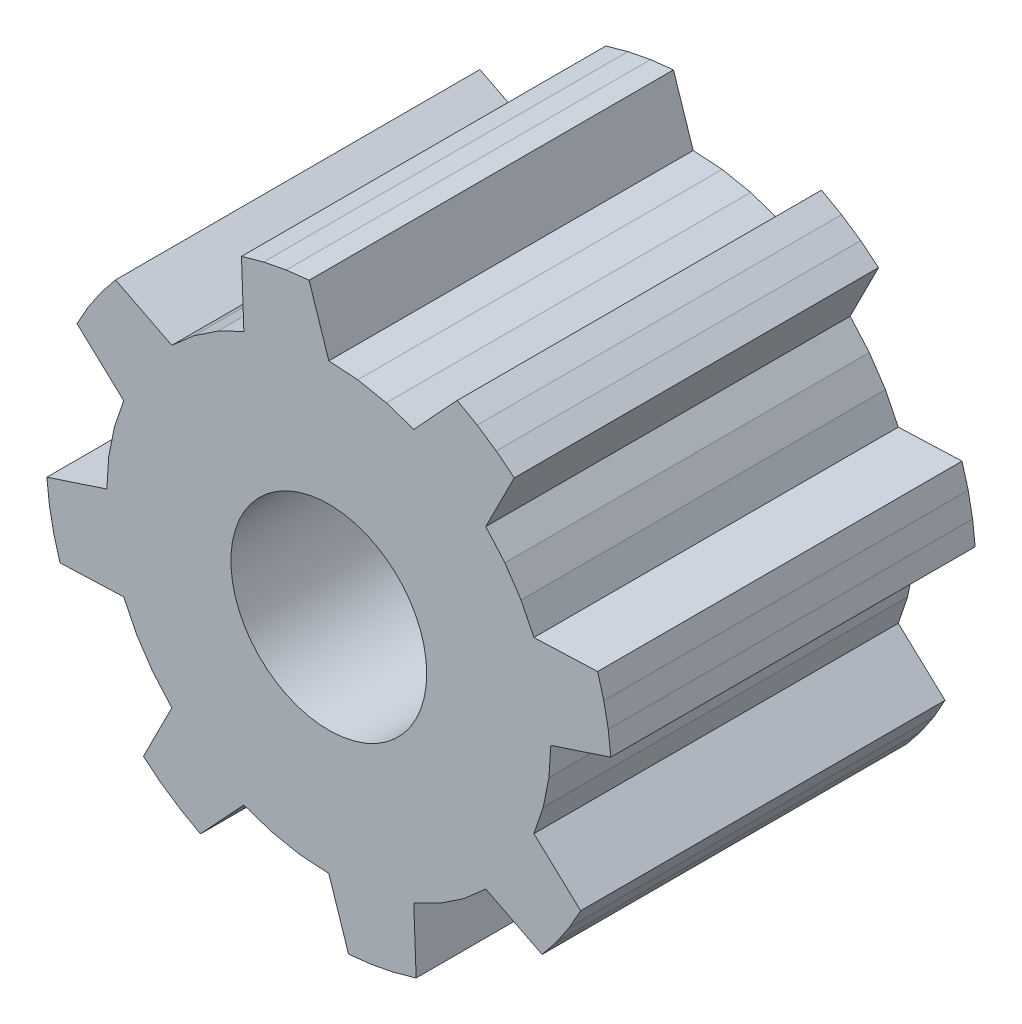
SolidWorks part; units mm, degrees
material "Green ABS"
ref_plane "Front Plane" through (0, 0, 0) normal (0, 0, 1) x (1, 0, 0)
ref_plane "Top Plane" through (0, 0, 0) normal (0, 1, 0) x (1, 0, 0)
ref_plane "Right Plane" through (0, 0, 0) normal (1, 0, 0) x (0, 0, -1)
sketch "Sketch2" plane through (0, 0, 0) normal (0, 0, 1) x (1, 0, 0)
  line L2 (4.8737, 0) -> (4.832, -0.6361)
  line L3 (4.832, -0.6361) -> (4.7076, -1.2614)
  line L7 (4.7076, -1.2614) -> (4.5027, -1.8651)
  line L18 (5.529, -2.8172) -> (5.2815, -3.2577)
  line L20 (4.5027, -1.8651) -> (5.529, -2.8172)
  line L25 (5.2815, -3.2577) -> (4.999, -3.6766)
  line L27 (4.6833, -4.0711) -> (3.4462, -3.4462)
  line L29 (4.999, -3.6766) -> (4.6833, -4.0711)
  line L30 (3.4462, -3.4462) -> (2.9669, -3.8666)
  line L34 (2.9669, -3.8666) -> (2.4369, -4.2208)
  line L37 (2.4369, -4.2208) -> (1.8651, -4.5027)
  line L43 (0, -4.8737) -> (-0.6361, -4.832)
  line L46 (-0.6361, -4.832) -> (-1.2614, -4.7076)
  line L49 (-1.2614, -4.7076) -> (-1.8651, -4.5027)
  line L56 (-3.4462, -3.4462) -> (-3.8666, -2.9669)
  line L57 (-3.8666, -2.9669) -> (-4.2208, -2.4369)
  line L61 (-4.2208, -2.4369) -> (-4.5027, -1.8651)
  line L68 (-4.8737, 0) -> (-4.832, 0.6361)
  line L69 (-4.832, 0.6361) -> (-4.7076, 1.2614)
  line L73 (-4.7076, 1.2614) -> (-4.5027, 1.8651)
  line L84 (1.9176, -5.9017) -> (1.4311, -6.0381)
  line L86 (1.8651, -4.5027) -> (1.9176, -5.9017)
  line L91 (1.4311, -6.0381) -> (0.9351, -6.1345)
  line L93 (0.4329, -6.1903) -> (0, -4.8737)
  line L95 (0.9351, -6.1345) -> (0.4329, -6.1903)
  line L96 (-2.8172, -5.529) -> (-3.2577, -5.2815)
  line L98 (-1.8651, -4.5027) -> (-2.8172, -5.529)
  line L100 (-3.2577, -5.2815) -> (-3.6766, -4.999)
  line L103 (-3.6766, -4.999) -> (-4.0711, -4.6833)
  line L104 (-4.0711, -4.6833) -> (-3.4462, -3.4462)
  line L108 (-5.9017, -1.9176) -> (-6.0381, -1.4311)
  line L110 (-4.5027, -1.8651) -> (-5.9017, -1.9176)
  line L115 (-6.0381, -1.4311) -> (-6.1345, -0.9351)
  line L117 (-6.1903, -0.4329) -> (-4.8737, 0)
  line L119 (-6.1345, -0.9351) -> (-6.1903, -0.4329)
  line L120 (-5.529, 2.8172) -> (-5.2815, 3.2577)
  line L122 (-4.5027, 1.8651) -> (-5.529, 2.8172)
  line L127 (-5.2815, 3.2577) -> (-4.999, 3.6766)
  line L129 (-4.6833, 4.0711) -> (-3.4462, 3.4462)
  line L131 (-4.999, 3.6766) -> (-4.6833, 4.0711)
  line L132 (-3.4462, 3.4462) -> (-2.9669, 3.8666)
  line L136 (-2.9669, 3.8666) -> (-2.4369, 4.2208)
  line L139 (-2.4369, 4.2208) -> (-1.8651, 4.5027)
  line L145 (0, 4.8737) -> (0.6361, 4.832)
  line L148 (0.6361, 4.832) -> (1.2614, 4.7076)
  line L151 (1.2614, 4.7076) -> (1.8651, 4.5027)
  line L158 (3.4462, 3.4462) -> (3.8666, 2.9669)
  line L159 (3.8666, 2.9669) -> (4.2208, 2.4369)
  line L163 (4.2208, 2.4369) -> (4.5027, 1.8651)
  line L171 (-1.9176, 5.9017) -> (-1.4311, 6.0381)
  line L173 (-1.8651, 4.5027) -> (-1.9176, 5.9017)
  line L178 (-1.4311, 6.0381) -> (-0.9351, 6.1345)
  line L180 (-0.4329, 6.1903) -> (0, 4.8737)
  line L182 (-0.9351, 6.1345) -> (-0.4329, 6.1903)
  line L183 (2.8172, 5.529) -> (3.2577, 5.2815)
  line L185 (1.8651, 4.5027) -> (2.8172, 5.529)
  line L187 (3.2577, 5.2815) -> (3.6766, 4.999)
  line L190 (3.6766, 4.999) -> (4.0711, 4.6833)
  line L191 (4.0711, 4.6833) -> (3.4462, 3.4462)
  line L195 (5.9017, 1.9176) -> (6.0381, 1.4311)
  line L197 (4.5027, 1.8651) -> (5.9017, 1.9176)
  line L199 (6.0381, 1.4311) -> (6.1345, 0.9351)
  line L202 (6.1345, 0.9351) -> (6.1903, 0.4329)
  line L203 (6.1903, 0.4329) -> (4.8737, 0)
  circle A0 centre (0, 0) radius 2.15
  dimension "D1" = 4.3
  dimension "D2" = 4.8737
  dimension "D3" = 6.2054
  dimension "D4" = 1.5125
  dimension "D5" = 1.9016
extrude "Boss-Extrude1" add sketch "Sketch2" along normal blind 8
